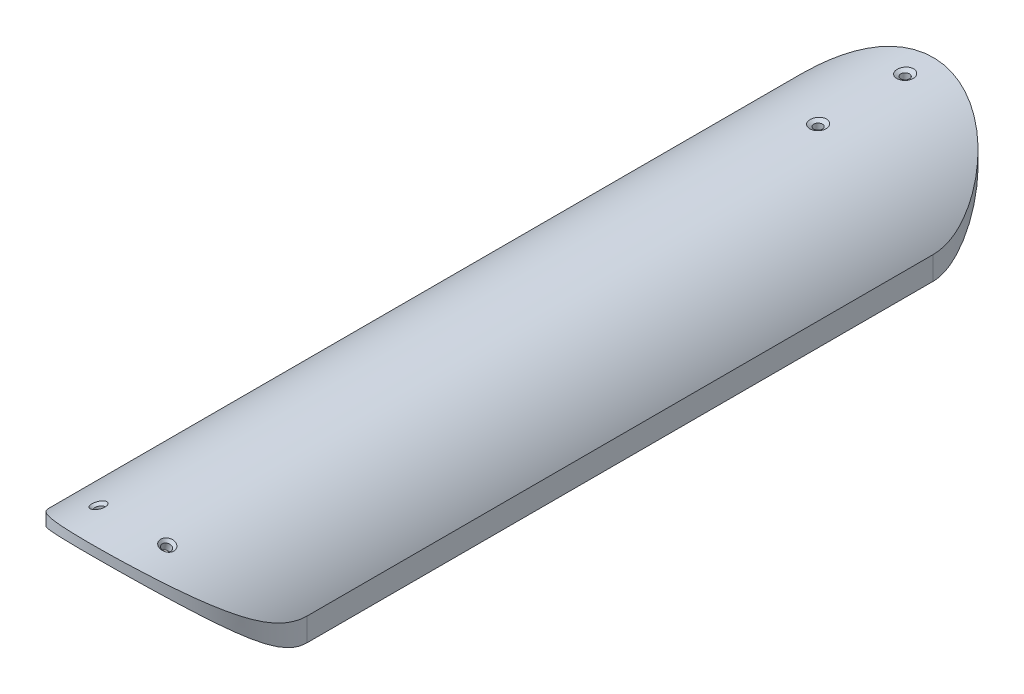
SolidWorks part; units mm, degrees
material "Hexcel AS4C (3000 Filaments)"
ref_plane "Plan de face" through (0, 0, 0) normal (0, 0, 1) x (1, 0, 0)
ref_plane "Plan de dessus" through (0, 0, 0) normal (0, 1, 0) x (1, 0, 0)
ref_plane "Plan de droite" through (0, 0, 0) normal (1, 0, 0) x (0, 0, -1)
sketch "Esquisse1" plane through (0, 0, 0) normal (0, 0, 1) x (1, 0, 0)
  line L0 (-91.6991, 0) -> (129.4182, 0) construction
  line L1 (0, 0) -> (-100.3512, 57.9378) construction
  line L2 (0, 0) -> (106.3084, 61.3772) construction
  line L3 (-38.5381, 22.25) -> (-38.5381, 0) construction
  line L4 (38.5381, 22.25) -> (38.5381, 0) construction
  line L5 (-38.5381, 22.25) -> (-38.5381, 13.9933)
  line L7 (38.5381, 22.25) -> (38.5381, 13.9933)
  arc A0 (-38.5381, 22.25) -> (38.5381, 22.25) centre (0, 0) cw
  arc A1 (-38.5381, 13.9933) -> (38.5381, 13.9933) centre (0, 0) cw
  dimension "D3" = 44.5
  dimension "D4" = 41
  dimension "D1" = 120
  dimension "D2" = 30
extrude "Boss.-Extru.1" add sketch "Esquisse1" along normal blind 300
sketch "Esquisse2" plane through (0, 0, 0) normal (0, 1, 0) x (1, 0, 0)
  line L0 (145.4118, -150) -> (-278.3086, -150) construction
  line L2 (138.6053, -261.46) -> (-356.8608, -261.46) construction
  line L3 (38.5381, 0) -> (-38.5381, 0) construction
  line L4 (0, -261.46) -> (0, -401.4728) construction
  line L5 (38.5381, -300) -> (38.5381, 0) construction
  line L6 (38.5381, -261.46) -> (70.8184, -261.46)
  line L7 (70.8184, -261.46) -> (70.8184, -316.2688)
  line L8 (70.8184, -316.2688) -> (-50.1181, -316.2688)
  line L9 (-50.1181, -316.2688) -> (-50.1181, -261.46)
  line L10 (-50.1181, -261.46) -> (-38.5381, -261.46)
  arc A0 (38.5381, -261.46) -> (-38.5381, -261.46) centre (0, -261.46) cw
  dimension "D1" = 111.46
  dimension "D2" = 150
extrude "Enlèv. mat.-Extru.1" cut sketch "Esquisse2" along normal through all
ref_plane "Plan1" through (0, 0, 150) normal (0, 0, 1) x (1, 0, 0)
mirror "Symétrie1" about plane through (0, 0, 150) normal (0, 0, 1) of "Enlèv. mat.-Extru.1"
hole_wizard "Dégagement M21" positions "Esquisse3D1" profile "Esquisse3" hole size "M2" standard "ISO" end condition through all
sketch3d "Esquisse3D1"
  point P28 (0.0019, 44.5, 10)
  dimension "D1" = 38.54
  dimension "D4" = 10
sketch "Esquisse3" plane through (0.0019, 44.5, 10) normal (0, 0, 1) x (-1, 0, 0)
  line L0 (0, 0) -> (0, 33.7047)
  line L1 (0, 33.7047) -> (1.55, 33.7047)
  line L2 (1.55, 33.7047) -> (1.55, 0.8372)
  line L3 (1.55, 0.8372) -> (3, 0)
  line L5 (3, 0) -> (0, 0)
  line L6 (-1.55, 0.8372) -> (-3, 0) construction
  line L11 (0, -6.35) -> (0, 107.95) construction
  dimension "Diamètre du perçage jusqu'au prochain" = 3.1
  dimension "Profondeur du perçage jusqu'au prochain" = 33.7047
  dimension "Diamètre du fraisage entrant" = 6
  dimension "Angle du fraisage entrant" = 120
pattern_linear "Répétition linéaire1" count 2 spacing 31 along (0, 0, 1) of "Dégagement M21"
hole_wizard "Dégagement M41" positions "Esquisse3D2" profile "Esquisse4" hole size "M4" standard "ISO"
sketch3d "Esquisse3D2"
  line L0 (0, 0, 0) -> (0, 0, 285) construction
  line L2 (0, 0, 285) -> (0, 124.6468, 285) construction
  line L5 (0, 0, 285) -> (12.2659, 42.7761, 285) construction
  line L7 (0, 0, 285) -> (-12.2659, 42.7761, 285) construction
  point P0 (-12.2659, 42.7761, 285)
  point P2 (12.2659, 42.7761, 285)
  dimension "D1" = 285
  dimension "D2" = 164
  dimension "D3" = 16
  dimension "D4" = 44.5
  dimension "D5" = 44.5
  dimension "D6" = 0
  dimension "D7" = 0
sketch "Esquisse4" plane through (-12.2659, 42.7761, 285) normal (0, 0, 1) x (-0.9613, -0.2756, 0)
  line L0 (0, 0) -> (0, 30.9313)
  line L1 (0, 30.9313) -> (1.55, 30)
  line L2 (1.55, 30) -> (1.55, 0.95)
  line L3 (1.55, 0.95) -> (2.5, 0)
  line L5 (2.5, 0) -> (0, 0)
  line L6 (-1.55, 0.95) -> (-2.5, 0) construction
  line L10 (0, 30.9313) -> (-1.55, 30) construction
  line L11 (0, -6.35) -> (0, 107.95) construction
  dimension "Diamètre du perçage" = 3.1
  dimension "Profondeur du perçage" = 30
  dimension "Diamètre du fraisage entrant" = 5
  dimension "Angle du fraisage entrant" = 90
  dimension "Angle de pointe" = 118
